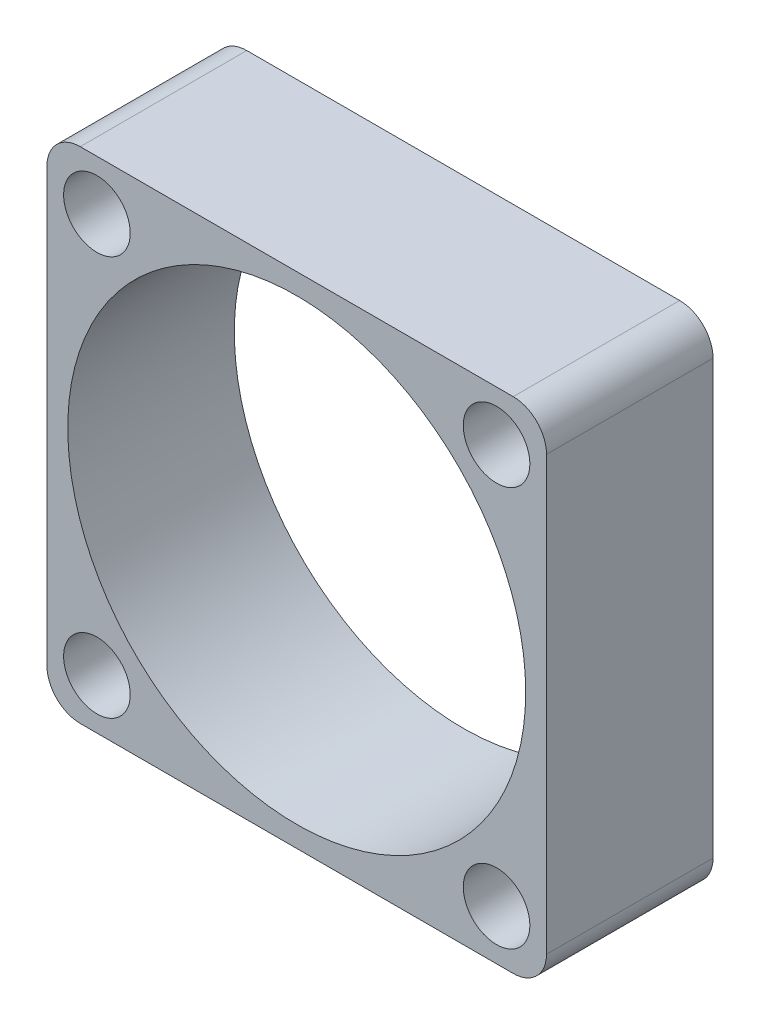
SolidWorks part; units mm, degrees
material "ABS PC"
ref_plane "Front Plane" through (0, 0, 0) normal (0, 0, 1) x (1, 0, 0)
ref_plane "Top Plane" through (0, 0, 0) normal (0, 1, 0) x (1, 0, 0)
ref_plane "Right Plane" through (0, 0, 0) normal (1, 0, 0) x (0, 0, -1)
sketch "Sketch1" plane through (0, 0, 0) normal (0, 0, 1) x (1, 0, 0)
  line L1 (0, 0) -> (30, 0)
  line L2 (0, 0) -> (0, 30)
  line L3 (0, 30) -> (30, 30)
  line L4 (30, 0) -> (30, 30)
  dimension "D1" = 30
  dimension "D2" = 30
extrude "Boss-Extrude1" add sketch "Sketch1" along normal blind 10
sketch "Sketch3" plane through (0, 0, 10) normal (0, 0, 1) x (1, 0, 0)
  line L0 (0, 15) -> (15, 15) construction
  line L1 (0, 30) -> (0, 0) construction
  line L2 (15, 15) -> (15, 0) construction
  line L3 (0, 0) -> (30, 0) construction
  line L4 (3, 27) -> (27, 3) construction
  line L5 (3, 3) -> (27, 27) construction
  circle A0 centre (15, 15) radius 13.75
  circle A1 centre (3, 27) radius 2
  circle A2 centre (27, 27) radius 2
  circle A3 centre (27, 3) radius 2
  circle A4 centre (3, 3) radius 2
  point P16 (0, 0)
  point P17 (2.571, 27)
  dimension "D1" = 27.5
  dimension "D6" = 4
  dimension "D3" = 24
extrude "Cut-Extrude1" cut sketch "Sketch3" against normal blind 10 contours A0 | A1 | A4 | A3 | A2
fillet "Fillet1" radius 2 4 edges at (0, 0, 5) (30, 0, 5) (0, 30, 5) (30, 30, 5)
